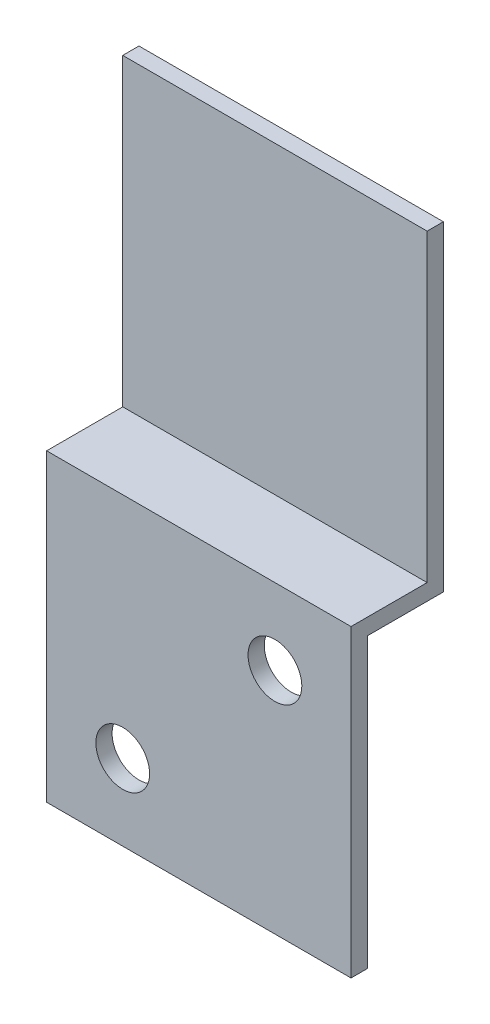
SolidWorks part; units mm, degrees
material "5052-H32"
ref_plane "Front Plane" through (0, 0, 0) normal (0, 0, 1) x (1, 0, 0)
ref_plane "Top Plane" through (0, 0, 0) normal (0, 1, 0) x (1, 0, 0)
ref_plane "Right Plane" through (0, 0, 0) normal (1, 0, 0) x (0, 0, -1)
sketch "Sketch1" plane through (0, 0, 0) normal (1, 0, 0) x (0, 0, -1)
  line L0 (0, 0) -> (0, -38.1)
  line L1 (0, -38.1) -> (-9.525, -38.1)
  line L2 (-9.525, -38.1) -> (-9.525, -76.2)
  line L3 (2.032, 0) -> (2.032, -40.132)
  line L4 (2.032, -40.132) -> (-7.493, -40.132)
  line L5 (-7.493, -40.132) -> (-7.493, -76.2)
  line L6 (-9.525, -76.2) -> (-7.493, -76.2)
  line L7 (0, 0) -> (2.032, 0)
  dimension "D1" = 2.032
  dimension "D2" = 38.1
  dimension "D3" = 76.2
  dimension "D4" = 9.525
extrude "Boss-Extrude1" add sketch "Sketch1" along normal blind 38.1
fillet "Fillet1" [suppressed] radius 2.032
fillet "Fillet2" [suppressed] radius 4.064
fillet "Fillet3" [suppressed] radius 3.175
sketch "Sketch2" plane through (0, 0, 9.525) normal (0, 0, 1) x (1, 0, 0)
  line L0 (38.1, -76.2) -> (0, -76.2) construction
  line L1 (0, -38.1) -> (0, -76.2) construction
  circle A0 centre (9.525, -66.675) radius 3.3655
  circle A1 centre (28.575, -47.625) radius 3.3655
  dimension "D1" = 9.525
  dimension "D4" = 6.731
  dimension "D2" = 9.525
  dimension "D3" = 28.575
  dimension "D5" = 28.575
extrude "Cut-Extrude1" cut sketch "Sketch2" against normal through all
